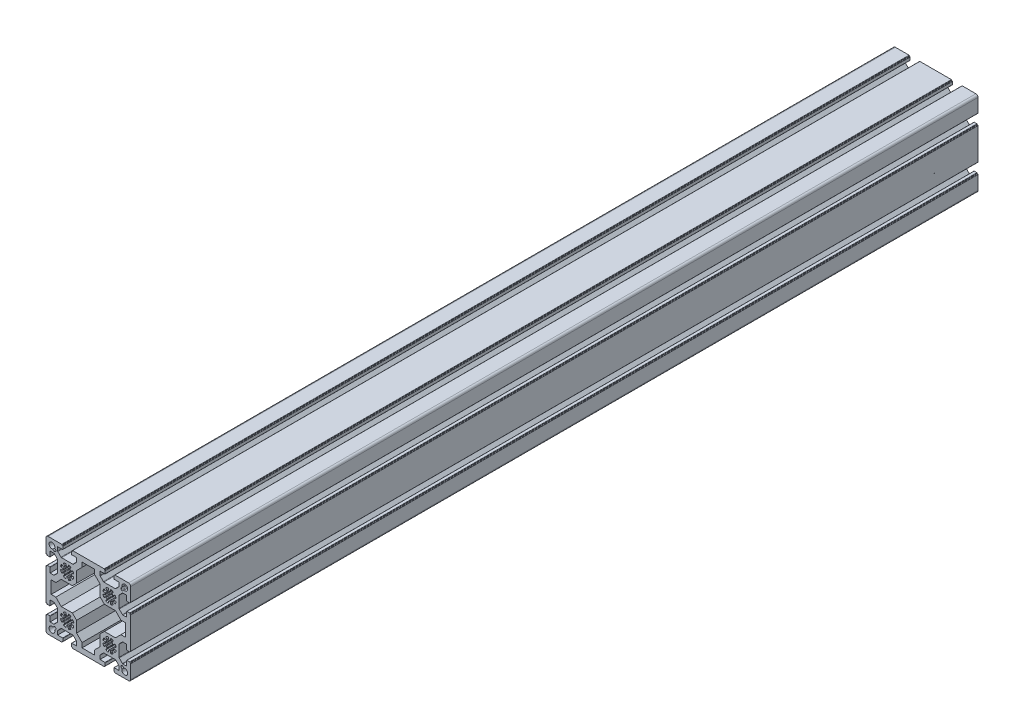
SolidWorks part; units mm, degrees
material "6063 T5"
ref_plane "Спереди" through (0, 0, 0) normal (0, 0, 1) x (1, 0, 0)
ref_plane "Сверху" through (0, 0, 0) normal (0, 1, 0) x (1, 0, 0)
ref_plane "Справа" through (0, 0, 0) normal (1, 0, 0) x (0, 0, -1)
sketch "Эскиз1" plane through (0, 0, 0) normal (0, 0, 1) x (1, 0, 0)
  line L0 (-19.98, 20.5457) -> (20.02, 20.5457) construction
  line L1 (-25, 11.25) -> (-25, 22.5)
  line L2 (-22.5, 25) -> (-11.25, 25)
  line L8 (0, 0) -> (25, 0) construction
  line L13 (0, 0) -> (0, -25) construction
  line L14 (0, -25) -> (25, -25) construction
  line L19 (25, 0) -> (25, -25) construction
  line L26 (-22.5383, 27.0237) -> (22.4617, 27.0237) construction
  line L29 (72.5, 25) -> (61.25, 25)
  line L30 (75, 11.25) -> (75, 22.5)
  line L31 (0, -50) -> (25, -50) construction
  line L32 (75, -61.25) -> (75, -72.5)
  line L33 (72.5, -75) -> (61.25, -75)
  line L49 (-22.5, -75) -> (-11.25, -75)
  line L50 (-31.9726, 22.6581) -> (-31.9726, -67.3419) construction
  line L51 (-25, -61.25) -> (-25, -72.5)
  line L52 (-25, -11.25) -> (-25, -38.75)
  line L53 (75, -11.25) -> (75, -38.75)
  line L55 (11.25, 25) -> (38.75, 25)
  line L57 (11.25, -75) -> (38.75, -75)
  line L59 (-22.4849, 32.3089) -> (67.5151, 32.3089) construction
  line L60 (25, -25) -> (0, 0) construction
  line L61 (-18.9, -32.45) -> (-18.9, -17.55)
  line L62 (-18.9, -17.55) -> (-13.4161, -17.55)
  line L63 (-13.4161, -17.55) -> (-6.9661, -11.1)
  line L64 (-6.9661, -11.1) -> (6.1, -11.1)
  line L65 (11.1, 6.9661) -> (11.1, -6.1)
  line L66 (17.55, 13.4161) -> (11.1, 6.9661)
  line L67 (17.55, 18.9) -> (17.55, 13.4161)
  line L68 (32.45, 18.9) -> (17.55, 18.9)
  line L70 (-18.9, -32.45) -> (-13.4161, -32.45)
  line L71 (-13.4161, -32.45) -> (-6.9661, -38.9)
  line L72 (-6.9661, -38.9) -> (6.1, -38.9)
  line L73 (11.1, -56.9661) -> (11.1, -43.9)
  line L74 (17.55, -63.4161) -> (11.1, -56.9661)
  line L75 (17.55, -68.9) -> (17.55, -63.4161)
  line L76 (32.45, -68.9) -> (17.55, -68.9)
  line L77 (32.45, 18.9) -> (32.45, 13.4161)
  line L78 (32.45, 13.4161) -> (38.9, 6.9661)
  line L79 (38.9, 6.9661) -> (38.9, -6.1)
  line L80 (56.9661, -11.1) -> (43.9, -11.1)
  line L81 (63.4161, -17.55) -> (56.9661, -11.1)
  line L82 (68.9, -17.55) -> (63.4161, -17.55)
  line L83 (68.9, -32.45) -> (68.9, -17.55)
  line L84 (68.9, -32.45) -> (63.4161, -32.45)
  line L85 (63.4161, -32.45) -> (56.9661, -38.9)
  line L86 (56.9661, -38.9) -> (43.9, -38.9)
  line L87 (38.9, -56.9661) -> (38.9, -43.9)
  line L88 (32.45, -63.4161) -> (38.9, -56.9661)
  line L89 (32.45, -68.9) -> (32.45, -63.4161)
  line L90 (-24.9768, 32.0132) -> (75.0232, 32.0132) construction
  line L91 (6.1, -11.1) -> (11.1, -6.1)
  line L92 (38.9, -6.1) -> (43.9, -11.1)
  line L93 (43.9, -38.9) -> (38.9, -43.9)
  line L94 (11.1, -43.9) -> (6.1, -38.9)
  line L95 (-18, 18) -> (-13.8988, 13.8988) construction
  line L96 (-18, 18) -> (-18, 14.6) construction
  line L97 (-16.9031, 14.7818) -> (-15.6665, 13.5452)
  line L98 (-14.2523, 13.5452) -> (-13.5452, 14.2523)
  line L99 (-13.5452, 15.6665) -> (-14.7818, 16.9031)
  line L100 (64.7818, 16.9031) -> (63.5452, 15.6665)
  line L101 (63.5452, 14.2523) -> (64.2523, 13.5452)
  line L102 (65.6665, 13.5452) -> (66.9031, 14.7818)
  line L103 (66.9031, -64.7818) -> (65.6665, -63.5452)
  line L104 (64.2523, -63.5452) -> (63.5452, -64.2523)
  line L105 (63.5452, -65.6665) -> (64.7818, -66.9031)
  line L106 (-14.7818, -66.9031) -> (-13.5452, -65.6665)
  line L107 (-13.5452, -64.2523) -> (-14.2523, -63.5452)
  line L108 (-15.6665, -63.5452) -> (-16.9031, -64.7818)
  arc A0 (-25, 22.5) -> (-22.5, 25) centre (-22.5, 22.5) cw
  arc A9 (75, 22.5) -> (72.5, 25) centre (72.5, 22.5) ccw
  arc A10 (75, -72.5) -> (72.5, -75) centre (72.5, -72.5) cw
  arc A19 (-25, -72.5) -> (-22.5, -75) centre (-22.5, -72.5) ccw
  arc A24 (-14.7818, 16.9031) -> (-16.9031, 14.7818) centre (-18, 18) ccw
  arc A25 (-13.5452, 14.2523) -> (-13.5452, 15.6665) centre (-14.2523, 14.9594) ccw
  arc A26 (-15.6665, 13.5452) -> (-14.2523, 13.5452) centre (-14.9594, 14.2523) ccw
  arc A27 (66.9031, 14.7818) -> (64.7818, 16.9031) centre (68, 18) ccw
  arc A28 (63.5452, 15.6665) -> (63.5452, 14.2523) centre (64.2523, 14.9594) ccw
  arc A29 (64.2523, 13.5452) -> (65.6665, 13.5452) centre (64.9594, 14.2523) ccw
  arc A30 (64.7818, -66.9031) -> (66.9031, -64.7818) centre (68, -68) ccw
  arc A31 (65.6665, -63.5452) -> (64.2523, -63.5452) centre (64.9594, -64.2523) ccw
  arc A32 (63.5452, -64.2523) -> (63.5452, -65.6665) centre (64.2523, -64.9594) ccw
  arc A33 (-16.9031, -64.7818) -> (-14.7818, -66.9031) centre (-18, -68) ccw
  arc A34 (-13.5452, -65.6665) -> (-13.5452, -64.2523) centre (-14.2523, -64.9594) ccw
  arc A35 (-14.2523, -63.5452) -> (-15.6665, -63.5452) centre (-14.9594, -64.2523) ccw
  point P5 (0, 0)
  point P30 (-12.8381, 14.9594)
  point P33 (-14.9594, 12.8381)
  point P43 (50, 0)
  point P69 (25, -25)
  point P81 (50, -50)
  point P82 (0, -50)
  point P107 (-18.9, -25)
  point P120 (25, 18.9)
  point P131 (25, -68.9)
  line B0 (-25, 11.25) -> (-25, 6.4)
  line B1 (-24.7, 6.1) -> (-24.3, 6.1)
  line B2 (-24, 5.8) -> (-24, 5.4)
  line B3 (-23.7, 5.1) -> (-20.5, 5.1)
  line B4 (-20.2, 5.4) -> (-20.2, 11.25)
  line B5 (-20.2, 11.25) -> (-15.8742, 11.25)
  line B6 (-15.1671, 10.9571) -> (-11.5029, 7.2929)
  line B7 (-11.21, 6.5858) -> (-11.21, -6.5858)
  line B8 (-11.21, 0) -> (-25, 0) construction
  line B9 (-15.1671, -10.9571) -> (-11.5029, -7.2929)
  line B10 (-20.2, -11.25) -> (-15.8742, -11.25)
  line B11 (-20.2, -5.4) -> (-20.2, -11.25)
  line B12 (-23.7, -5.1) -> (-20.5, -5.1)
  line B13 (-24, -5.8) -> (-24, -5.4)
  line B14 (-24.7, -6.1) -> (-24.3, -6.1)
  line B15 (-25, -11.25) -> (-25, -6.4)
  arc B16 (-20.5, 5.1) -> (-20.2, 5.4) centre (-20.5, 5.4) ccw
  arc B17 (-24, 5.4) -> (-23.7, 5.1) centre (-23.7, 5.4) ccw
  arc B18 (-24.3, 6.1) -> (-24, 5.8) centre (-24.3, 5.8) cw
  arc B19 (-25, 6.4) -> (-24.7, 6.1) centre (-24.7, 6.4) ccw
  arc B20 (-11.5029, 7.2929) -> (-11.21, 6.5858) centre (-12.21, 6.5858) cw
  arc B21 (-15.8742, 11.25) -> (-15.1671, 10.9571) centre (-15.8742, 10.25) cw
  arc B22 (-15.8742, -11.25) -> (-15.1671, -10.9571) centre (-15.8742, -10.25) ccw
  arc B23 (-11.5029, -7.2929) -> (-11.21, -6.5858) centre (-12.21, -6.5858) ccw
  arc B24 (-25, -6.4) -> (-24.7, -6.1) centre (-24.7, -6.4) cw
  arc B25 (-24.3, -6.1) -> (-24, -5.8) centre (-24.3, -5.8) ccw
  arc B26 (-24, -5.4) -> (-23.7, -5.1) centre (-23.7, -5.4) cw
  arc B27 (-20.5, -5.1) -> (-20.2, -5.4) centre (-20.5, -5.4) cw
  line B28 (0, 0) -> (3.6062, 3.6062) construction
  line B29 (1.3637, 7.358) -> (1.0164, 5.4842)
  line B30 (3.1592, 4.5967) -> (4.2386, 6.1672)
  line B31 (0, 0) -> (0, 5.1) construction
  arc B32 (0.478, -5.0776) -> (-0.478, -5.0776) centre (0, 0) cw
  arc B33 (-6.8804, -4.0816) -> (-7.7513, -1.979) centre (0, 0) cw
  arc B34 (3.9283, 3.2524) -> (3.2524, 3.9283) centre (0, 0) ccw
  arc B35 (4.0816, 6.8804) -> (1.979, 7.7513) centre (0, 0) ccw
  arc B36 (0.478, 5.0776) -> (-0.478, 5.0776) centre (0, 0) ccw
  line B37 (-1.3637, 7.358) -> (-1.0164, 5.4842)
  arc B38 (4.0816, -6.8804) -> (1.979, -7.7513) centre (0, 0) cw
  arc B39 (-3.9283, -3.2524) -> (-3.2524, -3.9283) centre (0, 0) ccw
  line B40 (-3.1592, -4.5967) -> (-4.2386, -6.1672)
  line B41 (0, 0) -> (6.3318, 0) construction
  line B42 (4.5967, 3.1592) -> (6.1672, 4.2386)
  line B43 (7.358, 1.3637) -> (5.4842, 1.0164)
  line B44 (-7.358, 1.3637) -> (-5.4842, 1.0164)
  line B45 (-4.5967, 3.1592) -> (-6.1672, 4.2386)
  line B46 (-3.1592, 4.5967) -> (-4.2386, 6.1672)
  line B47 (7.358, -1.3637) -> (5.4842, -1.0164)
  line B48 (4.5967, -3.1592) -> (6.1672, -4.2386)
  line B49 (3.1592, -4.5967) -> (4.2386, -6.1672)
  line B50 (1.3637, -7.358) -> (1.0164, -5.4842)
  line B51 (-1.3637, -7.358) -> (-1.0164, -5.4842)
  line B52 (-4.5967, -3.1592) -> (-6.1672, -4.2386)
  line B53 (-7.358, -1.3637) -> (-5.4842, -1.0164)
  arc B54 (5.0776, 0.478) -> (5.0776, -0.478) centre (0, 0) cw
  arc B55 (6.8804, 4.0816) -> (7.7513, 1.979) centre (0, 0) cw
  arc B56 (-5.0776, 0.478) -> (-5.0776, -0.478) centre (0, 0) ccw
  arc B57 (-6.8804, 4.0816) -> (-7.7513, 1.979) centre (0, 0) ccw
  arc B58 (-3.9283, 3.2524) -> (-3.2524, 3.9283) centre (0, 0) cw
  arc B59 (-4.0816, 6.8804) -> (-1.979, 7.7513) centre (0, 0) cw
  arc B60 (6.8804, -4.0816) -> (7.7513, -1.979) centre (0, 0) ccw
  arc B61 (3.9283, -3.2524) -> (3.2524, -3.9283) centre (0, 0) cw
  arc B62 (-4.0816, -6.8804) -> (-1.979, -7.7513) centre (0, 0) ccw
  arc B63 (5.0776, 0.478) -> (5.4842, 1.0164) centre (5.5754, 0.5248) cw
  arc B64 (5.4842, -1.0164) -> (5.0776, -0.478) centre (5.5754, -0.5248) cw
  arc B65 (7.7513, -1.979) -> (7.358, -1.3637) centre (7.2669, -1.8554) ccw
  arc B66 (6.8804, -4.0816) -> (6.1672, -4.2386) centre (6.4504, -3.8265) cw
  arc B67 (3.9283, -3.2524) -> (4.5967, -3.1592) centre (4.3135, -3.5713) cw
  arc B68 (3.2524, -3.9283) -> (3.1592, -4.5967) centre (3.5713, -4.3135) ccw
  arc B69 (4.0816, -6.8804) -> (4.2386, -6.1672) centre (3.8265, -6.4504) ccw
  arc B70 (1.979, -7.7513) -> (1.3637, -7.358) centre (1.8554, -7.2669) cw
  arc B71 (0.478, -5.0776) -> (1.0164, -5.4842) centre (0.5248, -5.5754) cw
  arc B72 (-0.478, -5.0776) -> (-1.0164, -5.4842) centre (-0.5248, -5.5754) ccw
  arc B73 (-1.979, -7.7513) -> (-1.3637, -7.358) centre (-1.8554, -7.2669) ccw
  arc B74 (-4.0816, -6.8804) -> (-4.2386, -6.1672) centre (-3.8265, -6.4504) cw
  arc B75 (-3.2524, -3.9283) -> (-3.1592, -4.5967) centre (-3.5713, -4.3135) cw
  arc B76 (-3.9283, -3.2524) -> (-4.5967, -3.1592) centre (-4.3135, -3.5713) ccw
  arc B77 (-6.8804, -4.0816) -> (-6.1672, -4.2386) centre (-6.4504, -3.8265) ccw
  arc B78 (-7.7513, -1.979) -> (-7.358, -1.3637) centre (-7.2669, -1.8554) cw
  arc B79 (-5.4842, -1.0164) -> (-5.0776, -0.478) centre (-5.5754, -0.5248) ccw
  arc B80 (-5.0776, 0.478) -> (-5.4842, 1.0164) centre (-5.5754, 0.5248) ccw
  arc B81 (-7.7513, 1.979) -> (-7.358, 1.3637) centre (-7.2669, 1.8554) ccw
  arc B82 (-6.8804, 4.0816) -> (-6.1672, 4.2386) centre (-6.4504, 3.8265) cw
  arc B83 (-3.9283, 3.2524) -> (-4.5967, 3.1592) centre (-4.3135, 3.5713) cw
  arc B84 (-3.2524, 3.9283) -> (-3.1592, 4.5967) centre (-3.5713, 4.3135) ccw
  arc B85 (-4.0816, 6.8804) -> (-4.2386, 6.1672) centre (-3.8265, 6.4504) ccw
  arc B86 (-1.979, 7.7513) -> (-1.3637, 7.358) centre (-1.8554, 7.2669) cw
  arc B87 (-1.0164, 5.4842) -> (-0.478, 5.0776) centre (-0.5248, 5.5754) ccw
  arc B88 (1.0164, 5.4842) -> (0.478, 5.0776) centre (0.5248, 5.5754) cw
  arc B89 (1.3637, 7.358) -> (1.979, 7.7513) centre (1.8554, 7.2669) cw
  arc B90 (4.2386, 6.1672) -> (4.0816, 6.8804) centre (3.8265, 6.4504) ccw
  arc B91 (3.1592, 4.5967) -> (3.2524, 3.9283) centre (3.5713, 4.3135) ccw
  arc B92 (4.5967, 3.1592) -> (3.9283, 3.2524) centre (4.3135, 3.5713) cw
  arc B93 (6.1672, 4.2386) -> (6.8804, 4.0816) centre (6.4504, 3.8265) cw
  arc B94 (7.7513, 1.979) -> (7.358, 1.3637) centre (7.2669, 1.8554) cw
  line B95 (11.25, 25) -> (6.4, 25)
  line B96 (6.1, 24.7) -> (6.1, 24.3)
  line B97 (5.8, 24) -> (5.4, 24)
  line B98 (5.1, 23.7) -> (5.1, 20.5)
  line B99 (5.4, 20.2) -> (11.25, 20.2)
  line B100 (11.25, 20.2) -> (11.25, 15.8742)
  line B101 (10.9571, 15.1671) -> (7.2929, 11.5029)
  line B102 (6.5858, 11.21) -> (-6.5858, 11.21)
  line B103 (0, 11.21) -> (0, 25) construction
  line B104 (-10.9571, 15.1671) -> (-7.2929, 11.5029)
  line B105 (-11.25, 20.2) -> (-11.25, 15.8742)
  line B106 (-5.4, 20.2) -> (-11.25, 20.2)
  line B107 (-5.1, 23.7) -> (-5.1, 20.5)
  line B108 (-5.8, 24) -> (-5.4, 24)
  line B109 (-6.1, 24.7) -> (-6.1, 24.3)
  line B110 (-11.25, 25) -> (-6.4, 25)
  arc B111 (5.1, 20.5) -> (5.4, 20.2) centre (5.4, 20.5) ccw
  arc B112 (5.4, 24) -> (5.1, 23.7) centre (5.4, 23.7) ccw
  arc B113 (6.1, 24.3) -> (5.8, 24) centre (5.8, 24.3) cw
  arc B114 (6.4, 25) -> (6.1, 24.7) centre (6.4, 24.7) ccw
  arc B115 (7.2929, 11.5029) -> (6.5858, 11.21) centre (6.5858, 12.21) cw
  arc B116 (11.25, 15.8742) -> (10.9571, 15.1671) centre (10.25, 15.8742) cw
  arc B117 (-11.25, 15.8742) -> (-10.9571, 15.1671) centre (-10.25, 15.8742) ccw
  arc B118 (-7.2929, 11.5029) -> (-6.5858, 11.21) centre (-6.5858, 12.21) ccw
  arc B119 (-6.4, 25) -> (-6.1, 24.7) centre (-6.4, 24.7) cw
  arc B120 (-6.1, 24.3) -> (-5.8, 24) centre (-5.8, 24.3) ccw
  arc B121 (-5.4, 24) -> (-5.1, 23.7) centre (-5.4, 23.7) cw
  arc B122 (-5.1, 20.5) -> (-5.4, 20.2) centre (-5.4, 20.5) cw
  line B123 (75, 11.25) -> (75, 6.4)
  line B124 (74.7, 6.1) -> (74.3, 6.1)
  line B125 (74, 5.8) -> (74, 5.4)
  line B126 (73.7, 5.1) -> (70.5, 5.1)
  line B127 (70.2, 5.4) -> (70.2, 11.25)
  line B128 (70.2, 11.25) -> (65.8742, 11.25)
  line B129 (65.1671, 10.9571) -> (61.5029, 7.2929)
  line B130 (61.21, 6.5858) -> (61.21, -6.5858)
  line B131 (61.21, 0) -> (75, 0) construction
  line B132 (65.1671, -10.9571) -> (61.5029, -7.2929)
  line B133 (70.2, -11.25) -> (65.8742, -11.25)
  line B134 (70.2, -5.4) -> (70.2, -11.25)
  line B135 (73.7, -5.1) -> (70.5, -5.1)
  line B136 (74, -5.8) -> (74, -5.4)
  line B137 (74.7, -6.1) -> (74.3, -6.1)
  line B138 (75, -11.25) -> (75, -6.4)
  arc B139 (70.5, 5.1) -> (70.2, 5.4) centre (70.5, 5.4) cw
  arc B140 (74, 5.4) -> (73.7, 5.1) centre (73.7, 5.4) cw
  arc B141 (74.3, 6.1) -> (74, 5.8) centre (74.3, 5.8) ccw
  arc B142 (75, 6.4) -> (74.7, 6.1) centre (74.7, 6.4) cw
  arc B143 (61.5029, 7.2929) -> (61.21, 6.5858) centre (62.21, 6.5858) ccw
  arc B144 (65.8742, 11.25) -> (65.1671, 10.9571) centre (65.8742, 10.25) ccw
  arc B145 (65.8742, -11.25) -> (65.1671, -10.9571) centre (65.8742, -10.25) cw
  arc B146 (61.5029, -7.2929) -> (61.21, -6.5858) centre (62.21, -6.5858) cw
  arc B147 (75, -6.4) -> (74.7, -6.1) centre (74.7, -6.4) ccw
  arc B148 (74.3, -6.1) -> (74, -5.8) centre (74.3, -5.8) cw
  arc B149 (74, -5.4) -> (73.7, -5.1) centre (73.7, -5.4) ccw
  arc B150 (70.5, -5.1) -> (70.2, -5.4) centre (70.5, -5.4) ccw
  line B151 (50, 0) -> (46.3938, 3.6062) construction
  line B152 (48.6363, 7.358) -> (48.9836, 5.4842)
  line B153 (46.8408, 4.5967) -> (45.7614, 6.1672)
  line B154 (50, 0) -> (50, 5.1) construction
  arc B155 (49.522, -5.0776) -> (50.478, -5.0776) centre (50, 0) ccw
  arc B156 (56.8804, -4.0816) -> (57.7513, -1.979) centre (50, 0) ccw
  arc B157 (46.0717, 3.2524) -> (46.7476, 3.9283) centre (50, 0) cw
  arc B158 (45.9184, 6.8804) -> (48.021, 7.7513) centre (50, 0) cw
  arc B159 (49.522, 5.0776) -> (50.478, 5.0776) centre (50, 0) cw
  line B160 (51.3637, 7.358) -> (51.0164, 5.4842)
  arc B161 (45.9184, -6.8804) -> (48.021, -7.7513) centre (50, 0) ccw
  arc B162 (53.9283, -3.2524) -> (53.2524, -3.9283) centre (50, 0) cw
  line B163 (53.1592, -4.5967) -> (54.2386, -6.1672)
  line B164 (50, 0) -> (43.6682, 0) construction
  line B165 (45.4033, 3.1592) -> (43.8328, 4.2386)
  line B166 (42.642, 1.3637) -> (44.5158, 1.0164)
  line B167 (57.358, 1.3637) -> (55.4842, 1.0164)
  line B168 (54.5967, 3.1592) -> (56.1672, 4.2386)
  line B169 (53.1592, 4.5967) -> (54.2386, 6.1672)
  line B170 (42.642, -1.3637) -> (44.5158, -1.0164)
  line B171 (45.4033, -3.1592) -> (43.8328, -4.2386)
  line B172 (46.8408, -4.5967) -> (45.7614, -6.1672)
  line B173 (48.6363, -7.358) -> (48.9836, -5.4842)
  line B174 (51.3637, -7.358) -> (51.0164, -5.4842)
  line B175 (54.5967, -3.1592) -> (56.1672, -4.2386)
  line B176 (57.358, -1.3637) -> (55.4842, -1.0164)
  arc B177 (44.9224, 0.478) -> (44.9224, -0.478) centre (50, 0) ccw
  arc B178 (43.1196, 4.0816) -> (42.2487, 1.979) centre (50, 0) ccw
  arc B179 (55.0776, 0.478) -> (55.0776, -0.478) centre (50, 0) cw
  arc B180 (56.8804, 4.0816) -> (57.7513, 1.979) centre (50, 0) cw
  arc B181 (53.9283, 3.2524) -> (53.2524, 3.9283) centre (50, 0) ccw
  arc B182 (54.0816, 6.8804) -> (51.979, 7.7513) centre (50, 0) ccw
  arc B183 (43.1196, -4.0816) -> (42.2487, -1.979) centre (50, 0) cw
  arc B184 (46.0717, -3.2524) -> (46.7476, -3.9283) centre (50, 0) ccw
  arc B185 (54.0816, -6.8804) -> (51.979, -7.7513) centre (50, 0) cw
  arc B186 (44.9224, 0.478) -> (44.5158, 1.0164) centre (44.4246, 0.5248) ccw
  arc B187 (44.5158, -1.0164) -> (44.9224, -0.478) centre (44.4246, -0.5248) ccw
  arc B188 (42.2487, -1.979) -> (42.642, -1.3637) centre (42.7331, -1.8554) cw
  arc B189 (43.1196, -4.0816) -> (43.8328, -4.2386) centre (43.5496, -3.8265) ccw
  arc B190 (46.0717, -3.2524) -> (45.4033, -3.1592) centre (45.6865, -3.5713) ccw
  arc B191 (46.7476, -3.9283) -> (46.8408, -4.5967) centre (46.4287, -4.3135) cw
  arc B192 (45.9184, -6.8804) -> (45.7614, -6.1672) centre (46.1735, -6.4504) cw
  arc B193 (48.021, -7.7513) -> (48.6363, -7.358) centre (48.1446, -7.2669) ccw
  arc B194 (49.522, -5.0776) -> (48.9836, -5.4842) centre (49.4752, -5.5754) ccw
  arc B195 (50.478, -5.0776) -> (51.0164, -5.4842) centre (50.5248, -5.5754) cw
  arc B196 (51.979, -7.7513) -> (51.3637, -7.358) centre (51.8554, -7.2669) cw
  arc B197 (54.0816, -6.8804) -> (54.2386, -6.1672) centre (53.8265, -6.4504) ccw
  arc B198 (53.2524, -3.9283) -> (53.1592, -4.5967) centre (53.5713, -4.3135) ccw
  arc B199 (53.9283, -3.2524) -> (54.5967, -3.1592) centre (54.3135, -3.5713) cw
  arc B200 (56.8804, -4.0816) -> (56.1672, -4.2386) centre (56.4504, -3.8265) cw
  arc B201 (57.7513, -1.979) -> (57.358, -1.3637) centre (57.2669, -1.8554) ccw
  arc B202 (55.4842, -1.0164) -> (55.0776, -0.478) centre (55.5754, -0.5248) cw
  arc B203 (55.0776, 0.478) -> (55.4842, 1.0164) centre (55.5754, 0.5248) cw
  arc B204 (57.7513, 1.979) -> (57.358, 1.3637) centre (57.2669, 1.8554) cw
  arc B205 (56.8804, 4.0816) -> (56.1672, 4.2386) centre (56.4504, 3.8265) ccw
  arc B206 (53.9283, 3.2524) -> (54.5967, 3.1592) centre (54.3135, 3.5713) ccw
  arc B207 (53.2524, 3.9283) -> (53.1592, 4.5967) centre (53.5713, 4.3135) cw
  arc B208 (54.0816, 6.8804) -> (54.2386, 6.1672) centre (53.8265, 6.4504) cw
  arc B209 (51.979, 7.7513) -> (51.3637, 7.358) centre (51.8554, 7.2669) ccw
  arc B210 (51.0164, 5.4842) -> (50.478, 5.0776) centre (50.5248, 5.5754) cw
  arc B211 (48.9836, 5.4842) -> (49.522, 5.0776) centre (49.4752, 5.5754) ccw
  arc B212 (48.6363, 7.358) -> (48.021, 7.7513) centre (48.1446, 7.2669) ccw
  arc B213 (45.7614, 6.1672) -> (45.9184, 6.8804) centre (46.1735, 6.4504) cw
  arc B214 (46.8408, 4.5967) -> (46.7476, 3.9283) centre (46.4287, 4.3135) cw
  arc B215 (45.4033, 3.1592) -> (46.0717, 3.2524) centre (45.6865, 3.5713) ccw
  arc B216 (43.8328, 4.2386) -> (43.1196, 4.0816) centre (43.5496, 3.8265) ccw
  arc B217 (42.2487, 1.979) -> (42.642, 1.3637) centre (42.7331, 1.8554) ccw
  line B218 (38.75, 25) -> (43.6, 25)
  line B219 (43.9, 24.7) -> (43.9, 24.3)
  line B220 (44.2, 24) -> (44.6, 24)
  line B221 (44.9, 23.7) -> (44.9, 20.5)
  line B222 (44.6, 20.2) -> (38.75, 20.2)
  line B223 (38.75, 20.2) -> (38.75, 15.8742)
  line B224 (39.0429, 15.1671) -> (42.7071, 11.5029)
  line B225 (43.4142, 11.21) -> (56.5858, 11.21)
  line B226 (50, 11.21) -> (50, 25) construction
  line B227 (60.9571, 15.1671) -> (57.2929, 11.5029)
  line B228 (61.25, 20.2) -> (61.25, 15.8742)
  line B229 (55.4, 20.2) -> (61.25, 20.2)
  line B230 (55.1, 23.7) -> (55.1, 20.5)
  line B231 (55.8, 24) -> (55.4, 24)
  line B232 (56.1, 24.7) -> (56.1, 24.3)
  line B233 (61.25, 25) -> (56.4, 25)
  arc B234 (44.9, 20.5) -> (44.6, 20.2) centre (44.6, 20.5) cw
  arc B235 (44.6, 24) -> (44.9, 23.7) centre (44.6, 23.7) cw
  arc B236 (43.9, 24.3) -> (44.2, 24) centre (44.2, 24.3) ccw
  arc B237 (43.6, 25) -> (43.9, 24.7) centre (43.6, 24.7) cw
  arc B238 (42.7071, 11.5029) -> (43.4142, 11.21) centre (43.4142, 12.21) ccw
  arc B239 (38.75, 15.8742) -> (39.0429, 15.1671) centre (39.75, 15.8742) ccw
  arc B240 (61.25, 15.8742) -> (60.9571, 15.1671) centre (60.25, 15.8742) cw
  arc B241 (57.2929, 11.5029) -> (56.5858, 11.21) centre (56.5858, 12.21) cw
  arc B242 (56.4, 25) -> (56.1, 24.7) centre (56.4, 24.7) ccw
  arc B243 (56.1, 24.3) -> (55.8, 24) centre (55.8, 24.3) cw
  arc B244 (55.4, 24) -> (55.1, 23.7) centre (55.4, 23.7) ccw
  arc B245 (55.1, 20.5) -> (55.4, 20.2) centre (55.4, 20.5) ccw
  line B246 (-25, -61.25) -> (-25, -56.4)
  line B247 (-24.7, -56.1) -> (-24.3, -56.1)
  line B248 (-24, -55.8) -> (-24, -55.4)
  line B249 (-23.7, -55.1) -> (-20.5, -55.1)
  line B250 (-20.2, -55.4) -> (-20.2, -61.25)
  line B251 (-20.2, -61.25) -> (-15.8742, -61.25)
  line B252 (-15.1671, -60.9571) -> (-11.5029, -57.2929)
  line B253 (-11.21, -56.5858) -> (-11.21, -43.4142)
  line B254 (-11.21, -50) -> (-25, -50) construction
  line B255 (-15.1671, -39.0429) -> (-11.5029, -42.7071)
  line B256 (-20.2, -38.75) -> (-15.8742, -38.75)
  line B257 (-20.2, -44.6) -> (-20.2, -38.75)
  line B258 (-23.7, -44.9) -> (-20.5, -44.9)
  line B259 (-24, -44.2) -> (-24, -44.6)
  line B260 (-24.7, -43.9) -> (-24.3, -43.9)
  line B261 (-25, -38.75) -> (-25, -43.6)
  arc B262 (-20.5, -55.1) -> (-20.2, -55.4) centre (-20.5, -55.4) cw
  arc B263 (-24, -55.4) -> (-23.7, -55.1) centre (-23.7, -55.4) cw
  arc B264 (-24.3, -56.1) -> (-24, -55.8) centre (-24.3, -55.8) ccw
  arc B265 (-25, -56.4) -> (-24.7, -56.1) centre (-24.7, -56.4) cw
  arc B266 (-11.5029, -57.2929) -> (-11.21, -56.5858) centre (-12.21, -56.5858) ccw
  arc B267 (-15.8742, -61.25) -> (-15.1671, -60.9571) centre (-15.8742, -60.25) ccw
  arc B268 (-15.8742, -38.75) -> (-15.1671, -39.0429) centre (-15.8742, -39.75) cw
  arc B269 (-11.5029, -42.7071) -> (-11.21, -43.4142) centre (-12.21, -43.4142) cw
  arc B270 (-25, -43.6) -> (-24.7, -43.9) centre (-24.7, -43.6) ccw
  arc B271 (-24.3, -43.9) -> (-24, -44.2) centre (-24.3, -44.2) cw
  arc B272 (-24, -44.6) -> (-23.7, -44.9) centre (-23.7, -44.6) ccw
  arc B273 (-20.5, -44.9) -> (-20.2, -44.6) centre (-20.5, -44.6) ccw
  line B274 (0, -50) -> (3.6062, -53.6062) construction
  line B275 (1.3637, -57.358) -> (1.0164, -55.4842)
  line B276 (3.1592, -54.5967) -> (4.2386, -56.1672)
  line B277 (0, -50) -> (0, -55.1) construction
  arc B278 (0.478, -44.9224) -> (-0.478, -44.9224) centre (0, -50) ccw
  arc B279 (-6.8804, -45.9184) -> (-7.7513, -48.021) centre (0, -50) ccw
  arc B280 (3.9283, -53.2524) -> (3.2524, -53.9283) centre (0, -50) cw
  arc B281 (4.0816, -56.8804) -> (1.979, -57.7513) centre (0, -50) cw
  arc B282 (0.478, -55.0776) -> (-0.478, -55.0776) centre (0, -50) cw
  line B283 (-1.3637, -57.358) -> (-1.0164, -55.4842)
  arc B284 (4.0816, -43.1196) -> (1.979, -42.2487) centre (0, -50) ccw
  arc B285 (-3.9283, -46.7476) -> (-3.2524, -46.0717) centre (0, -50) cw
  line B286 (-3.1592, -45.4033) -> (-4.2386, -43.8328)
  line B287 (0, -50) -> (6.3318, -50) construction
  line B288 (4.5967, -53.1592) -> (6.1672, -54.2386)
  line B289 (7.358, -51.3637) -> (5.4842, -51.0164)
  line B290 (-7.358, -51.3637) -> (-5.4842, -51.0164)
  line B291 (-4.5967, -53.1592) -> (-6.1672, -54.2386)
  line B292 (-3.1592, -54.5967) -> (-4.2386, -56.1672)
  line B293 (7.358, -48.6363) -> (5.4842, -48.9836)
  line B294 (4.5967, -46.8408) -> (6.1672, -45.7614)
  line B295 (3.1592, -45.4033) -> (4.2386, -43.8328)
  line B296 (1.3637, -42.642) -> (1.0164, -44.5158)
  line B297 (-1.3637, -42.642) -> (-1.0164, -44.5158)
  line B298 (-4.5967, -46.8408) -> (-6.1672, -45.7614)
  line B299 (-7.358, -48.6363) -> (-5.4842, -48.9836)
  arc B300 (5.0776, -50.478) -> (5.0776, -49.522) centre (0, -50) ccw
  arc B301 (6.8804, -54.0816) -> (7.7513, -51.979) centre (0, -50) ccw
  arc B302 (-5.0776, -50.478) -> (-5.0776, -49.522) centre (0, -50) cw
  arc B303 (-6.8804, -54.0816) -> (-7.7513, -51.979) centre (0, -50) cw
  arc B304 (-3.9283, -53.2524) -> (-3.2524, -53.9283) centre (0, -50) ccw
  arc B305 (-4.0816, -56.8804) -> (-1.979, -57.7513) centre (0, -50) ccw
  arc B306 (6.8804, -45.9184) -> (7.7513, -48.021) centre (0, -50) cw
  arc B307 (3.9283, -46.7476) -> (3.2524, -46.0717) centre (0, -50) ccw
  arc B308 (-4.0816, -43.1196) -> (-1.979, -42.2487) centre (0, -50) cw
  arc B309 (5.0776, -50.478) -> (5.4842, -51.0164) centre (5.5754, -50.5248) ccw
  arc B310 (5.4842, -48.9836) -> (5.0776, -49.522) centre (5.5754, -49.4752) ccw
  arc B311 (7.7513, -48.021) -> (7.358, -48.6363) centre (7.2669, -48.1446) cw
  arc B312 (6.8804, -45.9184) -> (6.1672, -45.7614) centre (6.4504, -46.1735) ccw
  arc B313 (3.9283, -46.7476) -> (4.5967, -46.8408) centre (4.3135, -46.4287) ccw
  arc B314 (3.2524, -46.0717) -> (3.1592, -45.4033) centre (3.5713, -45.6865) cw
  arc B315 (4.0816, -43.1196) -> (4.2386, -43.8328) centre (3.8265, -43.5496) cw
  arc B316 (1.979, -42.2487) -> (1.3637, -42.642) centre (1.8554, -42.7331) ccw
  arc B317 (0.478, -44.9224) -> (1.0164, -44.5158) centre (0.5248, -44.4246) ccw
  arc B318 (-0.478, -44.9224) -> (-1.0164, -44.5158) centre (-0.5248, -44.4246) cw
  arc B319 (-1.979, -42.2487) -> (-1.3637, -42.642) centre (-1.8554, -42.7331) cw
  arc B320 (-4.0816, -43.1196) -> (-4.2386, -43.8328) centre (-3.8265, -43.5496) ccw
  arc B321 (-3.2524, -46.0717) -> (-3.1592, -45.4033) centre (-3.5713, -45.6865) ccw
  arc B322 (-3.9283, -46.7476) -> (-4.5967, -46.8408) centre (-4.3135, -46.4287) cw
  arc B323 (-6.8804, -45.9184) -> (-6.1672, -45.7614) centre (-6.4504, -46.1735) cw
  arc B324 (-7.7513, -48.021) -> (-7.358, -48.6363) centre (-7.2669, -48.1446) ccw
  arc B325 (-5.4842, -48.9836) -> (-5.0776, -49.522) centre (-5.5754, -49.4752) cw
  arc B326 (-5.0776, -50.478) -> (-5.4842, -51.0164) centre (-5.5754, -50.5248) cw
  arc B327 (-7.7513, -51.979) -> (-7.358, -51.3637) centre (-7.2669, -51.8554) cw
  arc B328 (-6.8804, -54.0816) -> (-6.1672, -54.2386) centre (-6.4504, -53.8265) ccw
  arc B329 (-3.9283, -53.2524) -> (-4.5967, -53.1592) centre (-4.3135, -53.5713) ccw
  arc B330 (-3.2524, -53.9283) -> (-3.1592, -54.5967) centre (-3.5713, -54.3135) cw
  arc B331 (-4.0816, -56.8804) -> (-4.2386, -56.1672) centre (-3.8265, -56.4504) cw
  arc B332 (-1.979, -57.7513) -> (-1.3637, -57.358) centre (-1.8554, -57.2669) ccw
  arc B333 (-1.0164, -55.4842) -> (-0.478, -55.0776) centre (-0.5248, -55.5754) cw
  arc B334 (1.0164, -55.4842) -> (0.478, -55.0776) centre (0.5248, -55.5754) ccw
  arc B335 (1.3637, -57.358) -> (1.979, -57.7513) centre (1.8554, -57.2669) ccw
  arc B336 (4.2386, -56.1672) -> (4.0816, -56.8804) centre (3.8265, -56.4504) cw
  arc B337 (3.1592, -54.5967) -> (3.2524, -53.9283) centre (3.5713, -54.3135) cw
  arc B338 (4.5967, -53.1592) -> (3.9283, -53.2524) centre (4.3135, -53.5713) ccw
  arc B339 (6.1672, -54.2386) -> (6.8804, -54.0816) centre (6.4504, -53.8265) ccw
  arc B340 (7.7513, -51.979) -> (7.358, -51.3637) centre (7.2669, -51.8554) ccw
  line B341 (50, -50) -> (46.3938, -53.6062) construction
  line B342 (48.6363, -57.358) -> (48.9836, -55.4842)
  line B343 (46.8408, -54.5967) -> (45.7614, -56.1672)
  line B344 (50, -50) -> (50, -55.1) construction
  arc B345 (49.522, -44.9224) -> (50.478, -44.9224) centre (50, -50) cw
  arc B346 (56.8804, -45.9184) -> (57.7513, -48.021) centre (50, -50) cw
  arc B347 (46.0717, -53.2524) -> (46.7476, -53.9283) centre (50, -50) ccw
  arc B348 (45.9184, -56.8804) -> (48.021, -57.7513) centre (50, -50) ccw
  arc B349 (49.522, -55.0776) -> (50.478, -55.0776) centre (50, -50) ccw
  line B350 (51.3637, -57.358) -> (51.0164, -55.4842)
  arc B351 (45.9184, -43.1196) -> (48.021, -42.2487) centre (50, -50) cw
  arc B352 (53.9283, -46.7476) -> (53.2524, -46.0717) centre (50, -50) ccw
  line B353 (53.1592, -45.4033) -> (54.2386, -43.8328)
  line B354 (50, -50) -> (43.6682, -50) construction
  line B355 (45.4033, -53.1592) -> (43.8328, -54.2386)
  line B356 (42.642, -51.3637) -> (44.5158, -51.0164)
  line B357 (57.358, -51.3637) -> (55.4842, -51.0164)
  line B358 (54.5967, -53.1592) -> (56.1672, -54.2386)
  line B359 (53.1592, -54.5967) -> (54.2386, -56.1672)
  line B360 (42.642, -48.6363) -> (44.5158, -48.9836)
  line B361 (45.4033, -46.8408) -> (43.8328, -45.7614)
  line B362 (46.8408, -45.4033) -> (45.7614, -43.8328)
  line B363 (48.6363, -42.642) -> (48.9836, -44.5158)
  line B364 (51.3637, -42.642) -> (51.0164, -44.5158)
  line B365 (54.5967, -46.8408) -> (56.1672, -45.7614)
  line B366 (57.358, -48.6363) -> (55.4842, -48.9836)
  arc B367 (44.9224, -50.478) -> (44.9224, -49.522) centre (50, -50) cw
  arc B368 (43.1196, -54.0816) -> (42.2487, -51.979) centre (50, -50) cw
  arc B369 (55.0776, -50.478) -> (55.0776, -49.522) centre (50, -50) ccw
  arc B370 (56.8804, -54.0816) -> (57.7513, -51.979) centre (50, -50) ccw
  arc B371 (53.9283, -53.2524) -> (53.2524, -53.9283) centre (50, -50) cw
  arc B372 (54.0816, -56.8804) -> (51.979, -57.7513) centre (50, -50) cw
  arc B373 (43.1196, -45.9184) -> (42.2487, -48.021) centre (50, -50) ccw
  arc B374 (46.0717, -46.7476) -> (46.7476, -46.0717) centre (50, -50) cw
  arc B375 (54.0816, -43.1196) -> (51.979, -42.2487) centre (50, -50) ccw
  arc B376 (44.9224, -50.478) -> (44.5158, -51.0164) centre (44.4246, -50.5248) cw
  arc B377 (44.5158, -48.9836) -> (44.9224, -49.522) centre (44.4246, -49.4752) cw
  arc B378 (42.2487, -48.021) -> (42.642, -48.6363) centre (42.7331, -48.1446) ccw
  arc B379 (43.1196, -45.9184) -> (43.8328, -45.7614) centre (43.5496, -46.1735) cw
  arc B380 (46.0717, -46.7476) -> (45.4033, -46.8408) centre (45.6865, -46.4287) cw
  arc B381 (46.7476, -46.0717) -> (46.8408, -45.4033) centre (46.4287, -45.6865) ccw
  arc B382 (45.9184, -43.1196) -> (45.7614, -43.8328) centre (46.1735, -43.5496) ccw
  arc B383 (48.021, -42.2487) -> (48.6363, -42.642) centre (48.1446, -42.7331) cw
  arc B384 (49.522, -44.9224) -> (48.9836, -44.5158) centre (49.4752, -44.4246) cw
  arc B385 (50.478, -44.9224) -> (51.0164, -44.5158) centre (50.5248, -44.4246) ccw
  arc B386 (51.979, -42.2487) -> (51.3637, -42.642) centre (51.8554, -42.7331) ccw
  arc B387 (54.0816, -43.1196) -> (54.2386, -43.8328) centre (53.8265, -43.5496) cw
  arc B388 (53.2524, -46.0717) -> (53.1592, -45.4033) centre (53.5713, -45.6865) cw
  arc B389 (53.9283, -46.7476) -> (54.5967, -46.8408) centre (54.3135, -46.4287) ccw
  arc B390 (56.8804, -45.9184) -> (56.1672, -45.7614) centre (56.4504, -46.1735) ccw
  arc B391 (57.7513, -48.021) -> (57.358, -48.6363) centre (57.2669, -48.1446) cw
  arc B392 (55.4842, -48.9836) -> (55.0776, -49.522) centre (55.5754, -49.4752) ccw
  arc B393 (55.0776, -50.478) -> (55.4842, -51.0164) centre (55.5754, -50.5248) ccw
  arc B394 (57.7513, -51.979) -> (57.358, -51.3637) centre (57.2669, -51.8554) ccw
  arc B395 (56.8804, -54.0816) -> (56.1672, -54.2386) centre (56.4504, -53.8265) cw
  arc B396 (53.9283, -53.2524) -> (54.5967, -53.1592) centre (54.3135, -53.5713) cw
  arc B397 (53.2524, -53.9283) -> (53.1592, -54.5967) centre (53.5713, -54.3135) ccw
  arc B398 (54.0816, -56.8804) -> (54.2386, -56.1672) centre (53.8265, -56.4504) ccw
  arc B399 (51.979, -57.7513) -> (51.3637, -57.358) centre (51.8554, -57.2669) cw
  arc B400 (51.0164, -55.4842) -> (50.478, -55.0776) centre (50.5248, -55.5754) ccw
  arc B401 (48.9836, -55.4842) -> (49.522, -55.0776) centre (49.4752, -55.5754) cw
  arc B402 (48.6363, -57.358) -> (48.021, -57.7513) centre (48.1446, -57.2669) cw
  arc B403 (45.7614, -56.1672) -> (45.9184, -56.8804) centre (46.1735, -56.4504) ccw
  arc B404 (46.8408, -54.5967) -> (46.7476, -53.9283) centre (46.4287, -54.3135) ccw
  arc B405 (45.4033, -53.1592) -> (46.0717, -53.2524) centre (45.6865, -53.5713) cw
  arc B406 (43.8328, -54.2386) -> (43.1196, -54.0816) centre (43.5496, -53.8265) cw
  arc B407 (42.2487, -51.979) -> (42.642, -51.3637) centre (42.7331, -51.8554) cw
  line B408 (11.25, -75) -> (6.4, -75)
  line B409 (6.1, -74.7) -> (6.1, -74.3)
  line B410 (5.8, -74) -> (5.4, -74)
  line B411 (5.1, -73.7) -> (5.1, -70.5)
  line B412 (5.4, -70.2) -> (11.25, -70.2)
  line B413 (11.25, -70.2) -> (11.25, -65.8742)
  line B414 (10.9571, -65.1671) -> (7.2929, -61.5029)
  line B415 (6.5858, -61.21) -> (-6.5858, -61.21)
  line B416 (0, -61.21) -> (0, -75) construction
  line B417 (-10.9571, -65.1671) -> (-7.2929, -61.5029)
  line B418 (-11.25, -70.2) -> (-11.25, -65.8742)
  line B419 (-5.4, -70.2) -> (-11.25, -70.2)
  line B420 (-5.1, -73.7) -> (-5.1, -70.5)
  line B421 (-5.8, -74) -> (-5.4, -74)
  line B422 (-6.1, -74.7) -> (-6.1, -74.3)
  line B423 (-11.25, -75) -> (-6.4, -75)
  arc B424 (5.1, -70.5) -> (5.4, -70.2) centre (5.4, -70.5) cw
  arc B425 (5.4, -74) -> (5.1, -73.7) centre (5.4, -73.7) cw
  arc B426 (6.1, -74.3) -> (5.8, -74) centre (5.8, -74.3) ccw
  arc B427 (6.4, -75) -> (6.1, -74.7) centre (6.4, -74.7) cw
  arc B428 (7.2929, -61.5029) -> (6.5858, -61.21) centre (6.5858, -62.21) ccw
  arc B429 (11.25, -65.8742) -> (10.9571, -65.1671) centre (10.25, -65.8742) ccw
  arc B430 (-11.25, -65.8742) -> (-10.9571, -65.1671) centre (-10.25, -65.8742) cw
  arc B431 (-7.2929, -61.5029) -> (-6.5858, -61.21) centre (-6.5858, -62.21) cw
  arc B432 (-6.4, -75) -> (-6.1, -74.7) centre (-6.4, -74.7) ccw
  arc B433 (-6.1, -74.3) -> (-5.8, -74) centre (-5.8, -74.3) cw
  arc B434 (-5.4, -74) -> (-5.1, -73.7) centre (-5.4, -73.7) ccw
  arc B435 (-5.1, -70.5) -> (-5.4, -70.2) centre (-5.4, -70.5) ccw
  line B436 (75, -61.25) -> (75, -56.4)
  line B437 (74.7, -56.1) -> (74.3, -56.1)
  line B438 (74, -55.8) -> (74, -55.4)
  line B439 (73.7, -55.1) -> (70.5, -55.1)
  line B440 (70.2, -55.4) -> (70.2, -61.25)
  line B441 (70.2, -61.25) -> (65.8742, -61.25)
  line B442 (65.1671, -60.9571) -> (61.5029, -57.2929)
  line B443 (61.21, -56.5858) -> (61.21, -43.4142)
  line B444 (61.21, -50) -> (75, -50) construction
  line B445 (65.1671, -39.0429) -> (61.5029, -42.7071)
  line B446 (70.2, -38.75) -> (65.8742, -38.75)
  line B447 (70.2, -44.6) -> (70.2, -38.75)
  line B448 (73.7, -44.9) -> (70.5, -44.9)
  line B449 (74, -44.2) -> (74, -44.6)
  line B450 (74.7, -43.9) -> (74.3, -43.9)
  line B451 (75, -38.75) -> (75, -43.6)
  arc B452 (70.5, -55.1) -> (70.2, -55.4) centre (70.5, -55.4) ccw
  arc B453 (74, -55.4) -> (73.7, -55.1) centre (73.7, -55.4) ccw
  arc B454 (74.3, -56.1) -> (74, -55.8) centre (74.3, -55.8) cw
  arc B455 (75, -56.4) -> (74.7, -56.1) centre (74.7, -56.4) ccw
  arc B456 (61.5029, -57.2929) -> (61.21, -56.5858) centre (62.21, -56.5858) cw
  arc B457 (65.8742, -61.25) -> (65.1671, -60.9571) centre (65.8742, -60.25) cw
  arc B458 (65.8742, -38.75) -> (65.1671, -39.0429) centre (65.8742, -39.75) ccw
  arc B459 (61.5029, -42.7071) -> (61.21, -43.4142) centre (62.21, -43.4142) ccw
  arc B460 (75, -43.6) -> (74.7, -43.9) centre (74.7, -43.6) cw
  arc B461 (74.3, -43.9) -> (74, -44.2) centre (74.3, -44.2) ccw
  arc B462 (74, -44.6) -> (73.7, -44.9) centre (73.7, -44.6) cw
  arc B463 (70.5, -44.9) -> (70.2, -44.6) centre (70.5, -44.6) cw
  line B464 (38.75, -75) -> (43.6, -75)
  line B465 (43.9, -74.7) -> (43.9, -74.3)
  line B466 (44.2, -74) -> (44.6, -74)
  line B467 (44.9, -73.7) -> (44.9, -70.5)
  line B468 (44.6, -70.2) -> (38.75, -70.2)
  line B469 (38.75, -70.2) -> (38.75, -65.8742)
  line B470 (39.0429, -65.1671) -> (42.7071, -61.5029)
  line B471 (43.4142, -61.21) -> (56.5858, -61.21)
  line B472 (50, -61.21) -> (50, -75) construction
  line B473 (60.9571, -65.1671) -> (57.2929, -61.5029)
  line B474 (61.25, -70.2) -> (61.25, -65.8742)
  line B475 (55.4, -70.2) -> (61.25, -70.2)
  line B476 (55.1, -73.7) -> (55.1, -70.5)
  line B477 (55.8, -74) -> (55.4, -74)
  line B478 (56.1, -74.7) -> (56.1, -74.3)
  line B479 (61.25, -75) -> (56.4, -75)
  arc B480 (44.9, -70.5) -> (44.6, -70.2) centre (44.6, -70.5) ccw
  arc B481 (44.6, -74) -> (44.9, -73.7) centre (44.6, -73.7) ccw
  arc B482 (43.9, -74.3) -> (44.2, -74) centre (44.2, -74.3) cw
  arc B483 (43.6, -75) -> (43.9, -74.7) centre (43.6, -74.7) ccw
  arc B484 (42.7071, -61.5029) -> (43.4142, -61.21) centre (43.4142, -62.21) cw
  arc B485 (38.75, -65.8742) -> (39.0429, -65.1671) centre (39.75, -65.8742) cw
  arc B486 (61.25, -65.8742) -> (60.9571, -65.1671) centre (60.25, -65.8742) ccw
  arc B487 (57.2929, -61.5029) -> (56.5858, -61.21) centre (56.5858, -62.21) ccw
  arc B488 (56.4, -75) -> (56.1, -74.7) centre (56.4, -74.7) cw
  arc B489 (56.1, -74.3) -> (55.8, -74) centre (55.8, -74.3) ccw
  arc B490 (55.4, -74) -> (55.1, -73.7) centre (55.4, -73.7) cw
  arc B491 (55.1, -70.5) -> (55.4, -70.2) centre (55.4, -70.5) cw
  dimension "D12" = 11.1
  dimension "D13" = 6.8
  dimension "D2" = 2.5
  dimension "D3" = 25
  dimension "D5" = 6.3
  dimension "D6" = 5.9
  dimension "D17" = 3
  dimension "D15" = 18
  dimension "D19" = 1
  dimension "D1" = 25
  dimension "D4" = 6.1
  dimension "D7" = 45
  dimension "D8" = 5
  dimension "D9" = 25
  dimension "D10" = 100
  dimension "D11" = 90
  dimension "D14" = 45
  dimension "D16" = 18
  dimension "D18" = 5.8
  dimension "D20" = 4
sketch_block_instance "8B(20,5PL)-1"
sketch_block "8B(20,5PL)" parameters "D7"=0.3, "D8"=1, "D1"=13.79, "D2"=4.8, "D3"=10.2, "D4"=22.5, "D5"=12.2, "D6"=135, "D9"=11.8, "D10"=4.85, "D11"=1.4, "D12"=1.65
sketch_block_instance "star_R5,1_R8-1"
sketch_block "star_R5,1_R8" parameters "D1"=10.2, "D5"=16, "D6"=0.5, "D2"=10.5, "D3"=24, "D4"=45
sketch_block_instance "8B(20,5PL)-11"
sketch_block_instance "8B(20,5PL)-12"
sketch_block_instance "star_R5,1_R8-3"
sketch_block_instance "8B(20,5PL)-13"
sketch_block_instance "8B(20,5PL)-18"
sketch_block_instance "star_R5,1_R8-6"
sketch_block_instance "star_R5,1_R8-7"
sketch_block_instance "8B(20,5PL)-19"
sketch_block_instance "8B(20,5PL)-20"
sketch_block_instance "8B(20,5PL)-21"
extrude "Бобышка-Вытянуть1" add sketch "Эскиз1" along normal blind 1000
